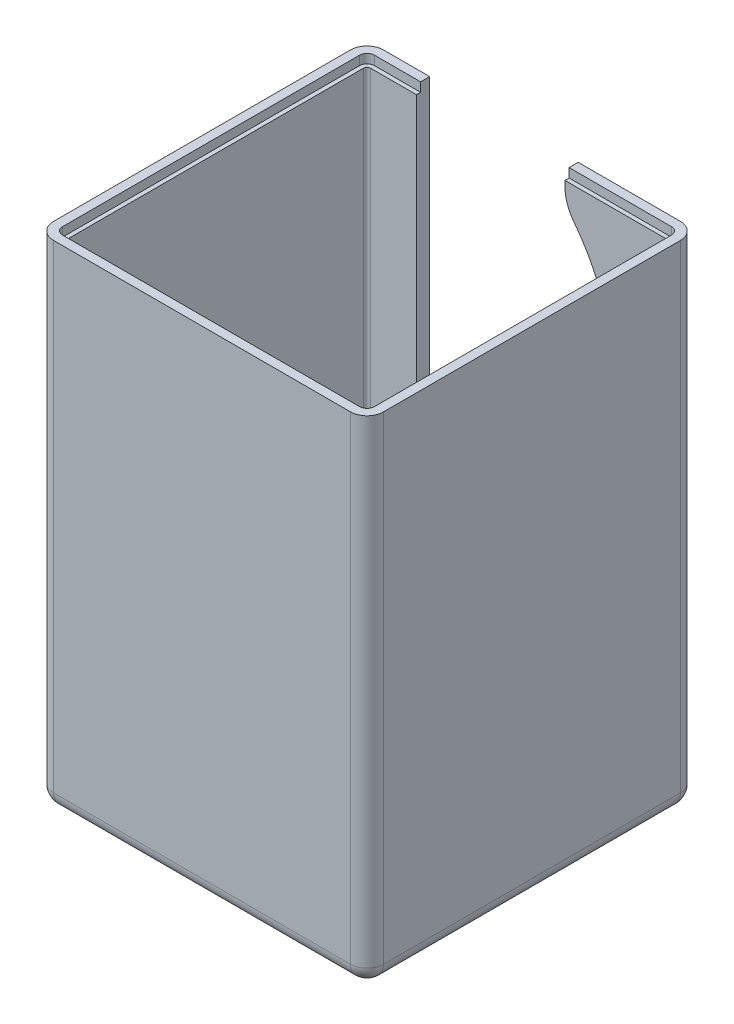
SolidWorks part; units mm, degrees
ref_plane "Front Plane" through (0, 0, 0) normal (0, 0, 1) x (1, 0, 0)
ref_plane "Top Plane" through (0, 0, 0) normal (0, 1, 0) x (1, 0, 0)
ref_plane "Right Plane" through (0, 0, 0) normal (1, 0, 0) x (0, 0, -1)
sketch "Sketch1" plane through (0, 0, 0) normal (0, 1, 0) x (1, 0, 0)
  line L1 (100, 100) -> (-100, 100)
  line L2 (100, 100) -> (100, -100)
  line L3 (100, -100) -> (-100, -100)
  line L4 (-100, 100) -> (-100, -100)
  line L5 (100, 100) -> (-100, -100) construction
  line L6 (100, -100) -> (-100, 100) construction
  point P0 (0, 0)
  dimension "D1" = 200
extrude "Boss-Extrude1" add sketch "Sketch1" along normal blind 300
fillet "Fillet1" radius 10 8 edges at (0, 0, 100) (100, 0, 0) (0, 0, -100) (-100, 0, 0) (-100, 150, 100) (-100, 150, -100) (100, 150, -100) (100, 150, 100)
shell "Shell1" thickness 8
sketch "Sketch2" plane through (0, 0, -100) normal (0, 0, -1) x (-1, 0, 0)
  line L0 (62, 100) -> (-28, 100)
  line L1 (62, 100) -> (62, 300)
  line L3 (62, 300) -> (-28, 300)
  line L4 (-90, 300) -> (90, 300) construction
  line L5 (-28, 282) -> (-28, 300)
  line L6 (-28, 100) -> (-28, 130)
  line L7 (100, 300) -> (100, 10) construction
  arc A7 (-28, 130) -> (-28, 282) centre (56.9706, 206) cw
  dimension "D3" = 18
  dimension "D5" = 114
  dimension "D1" = 200
  dimension "D2" = 90
  dimension "D4" = 30
  dimension "D6" = 38
extrude "Cut-Extrude1" cut sketch "Sketch2" against normal blind 44
fillet "Fillet2" radius 25 1 edges at (28, 130, -96)
fillet "Fillet3" radius 25 1 edges at (28, 282, -96)
sketch "Sketch3" plane through (0, 300, 0) normal (0, 1, 0) x (1, 0, 0)
  line L0 (90, 92) -> (28, 92) construction
  line L1 (90, 92) -> (28, 92)
  line L2 (90, 92) -> (-90, 92) construction
  line L3 (-92, 90) -> (-92, -90) construction
  line L4 (-90, -92) -> (90, -92) construction
  line L5 (92, -90) -> (92, 90) construction
  line L6 (90, 92) -> (-90, 92)
  line L7 (-92, 90) -> (-92, -90)
  line L8 (-90, -92) -> (90, -92)
  line L9 (92, -90) -> (92, 90)
  line L10 (90, 94.5) -> (-90, 94.5)
  line L11 (-94.5, 90) -> (-94.5, -90)
  line L12 (-90, -94.5) -> (90, -94.5)
  line L13 (94.5, -90) -> (94.5, 90)
  arc A0 (-90, 92) -> (-92, 90) centre (-90, 90) ccw construction
  arc A1 (-92, -90) -> (-90, -92) centre (-90, -90) ccw construction
  arc A2 (90, -92) -> (92, -90) centre (90, -90) ccw construction
  arc A3 (92, 90) -> (90, 92) centre (90, 90) ccw construction
  arc A4 (-90, 92) -> (-92, 90) centre (-90, 90) ccw
  arc A5 (-92, -90) -> (-90, -92) centre (-90, -90) ccw
  arc A6 (90, -92) -> (92, -90) centre (90, -90) ccw
  arc A7 (92, 90) -> (90, 92) centre (90, 90) ccw
  arc A8 (-90, 94.5) -> (-94.5, 90) centre (-90, 90) ccw
  arc A9 (-94.5, -90) -> (-90, -94.5) centre (-90, -90) ccw
  arc A10 (90, -94.5) -> (94.5, -90) centre (90, -90) ccw
  arc A11 (94.5, 90) -> (90, 94.5) centre (90, 90) ccw
  line M11 (28, 100) -> (28, 92)
  line M12 (28, 92) -> (90, 92)
  arc M13 (90, 92) -> (92, 90) centre (90, 90) cw
  line M14 (92, 90) -> (92, -90)
  arc M15 (92, -90) -> (90, -92) centre (90, -90) cw
  line M16 (90, -92) -> (-90, -92)
  arc M17 (-90, -92) -> (-92, -90) centre (-90, -90) cw
  line M18 (-92, -90) -> (-92, 90)
  arc M19 (-92, 90) -> (-90, 92) centre (-90, 90) cw
  line M20 (-90, 92) -> (-62, 92)
  line M21 (-62, 92) -> (-62, 100)
  dimension "D1" = 2.5
extrude "Cut-Extrude2" cut sketch "Sketch3" against normal blind 5.5 contours L13 A11 L10 A8 L11 A9 L12 A10 M11 M12 M13 M14 M15 M16 M17 M18 M19 M20 M21
